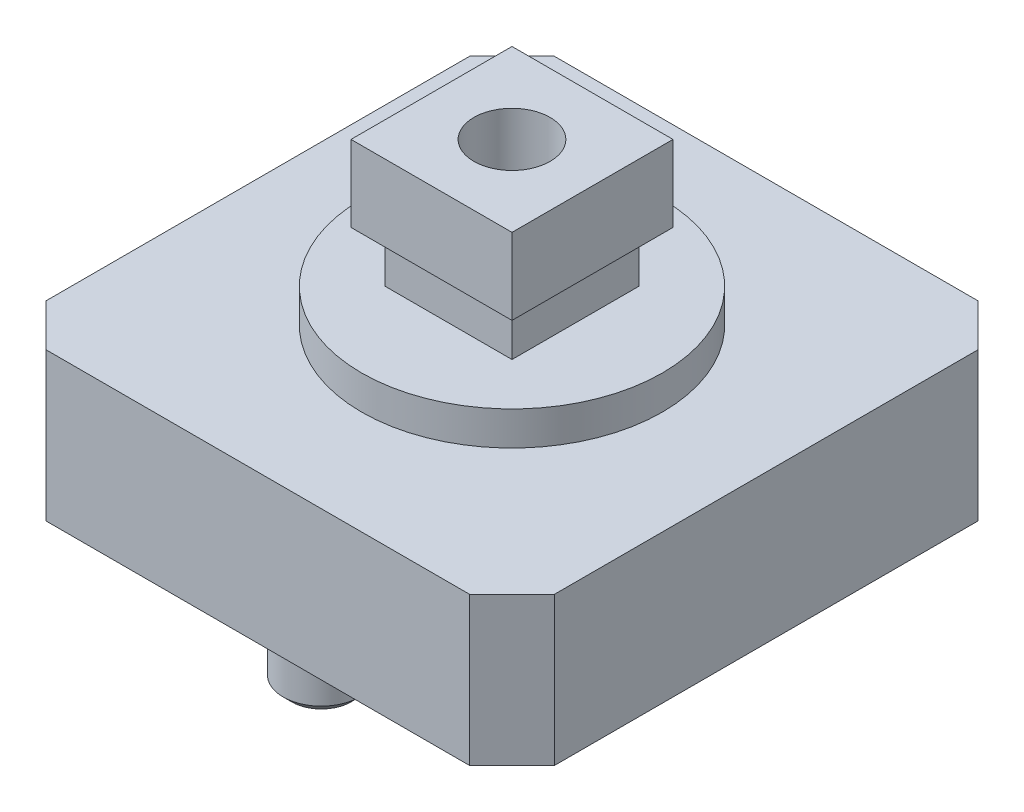
SolidWorks part; units mm, degrees
ref_plane "Front Plane" through (0, 0, 0) normal (0, 0, 1) x (1, 0, 0)
ref_plane "Top Plane" through (0, 0, 0) normal (0, 1, 0) x (1, 0, 0)
ref_plane "Right Plane" through (0, 0, 0) normal (1, 0, 0) x (0, 0, -1)
sketch "Sketch1" plane through (0, 0, 0) normal (0, 1, 0) x (1, 0, 0)
  line L0 (-6, 5) -> (-5, 6)
  line L1 (-5, 6) -> (5, 6)
  line L2 (-6, 5) -> (-6, -5)
  line L3 (-5, -6) -> (5, -6)
  line L4 (6, 5) -> (6, -5)
  line L5 (-6, 6) -> (6, -6) construction
  line L6 (-6, -6) -> (6, 6) construction
  line L7 (-6, -5) -> (-5, -6)
  line L8 (5, -6) -> (6, -5)
  line L9 (5, 6) -> (6, 5)
  point P0 (0, 0)
  dimension "D1" = 12
  dimension "D2" = 12
extrude "Boss-Extrude1" add sketch "Sketch1" along normal blind 3.5
sketch "Sketch2" plane through (0, 0, 0) normal (0, -1, 0) x (1, 0, 0)
  line L0 (-1000, 0) -> (49000, 0) construction
  circle A0 centre (0, -4.5) radius 0.9
  circle A1 centre (0, 4.5) radius 0.9
  dimension "D1" = 1.8
  dimension "D2" = 4.5
extrude "Boss-Extrude2" add sketch "Sketch2" along normal blind 1.6
chamfer "Chamfer1" distance 0.2 angle 45 2 edges at (0, -1.6, 5.4) (0, -1.6, -5.4)
sketch "Sketch3" plane through (0, 3.5, 0) normal (0, 1, 0) x (1, 0, 0)
  circle A0 centre (0, 0) radius 3.55
  dimension "D1" = 7.1
extrude "Boss-Extrude3" add sketch "Sketch3" along normal blind 0.8
sketch "Sketch4" plane through (0, 4.3, 0) normal (0, 1, 0) x (1, 0, 0)
  line L1 (1.5, -1.5) -> (-1.5, -1.5)
  line L2 (1.5, -1.5) -> (1.5, 1.5)
  line L3 (1.5, 1.5) -> (-1.5, 1.5)
  line L4 (-1.5, -1.5) -> (-1.5, 1.5)
  line L5 (1.5, -1.5) -> (-1.5, 1.5) construction
  line L6 (1.5, 1.5) -> (-1.5, -1.5) construction
  point P0 (0, 0)
  dimension "D1" = 3
  dimension "D2" = 3
extrude "Boss-Extrude4" add sketch "Sketch4" along normal blind 1.2
sketch "Sketch5" plane through (0, 5.5, 0) normal (0, 1, 0) x (1, 0, 0)
  line L1 (1.9, -1.9) -> (-1.9, -1.9)
  line L2 (1.9, -1.9) -> (1.9, 1.9)
  line L3 (1.9, 1.9) -> (-1.9, 1.9)
  line L4 (-1.9, -1.9) -> (-1.9, 1.9)
  line L5 (1.9, -1.9) -> (-1.9, 1.9) construction
  line L6 (1.9, 1.9) -> (-1.9, -1.9) construction
  point P0 (0, 0)
  dimension "D1" = 3.8
  dimension "D2" = 3.8
extrude "Boss-Extrude5" add sketch "Sketch5" along normal blind 1.8
sketch "Sketch6" plane through (0, 7.3, 0) normal (0, 1, 0) x (1, 0, 0)
  circle A0 centre (0, 0) radius 0.9
  dimension "D1" = 1.8
extrude "Cut-Extrude1" cut sketch "Sketch6" against normal blind 2
